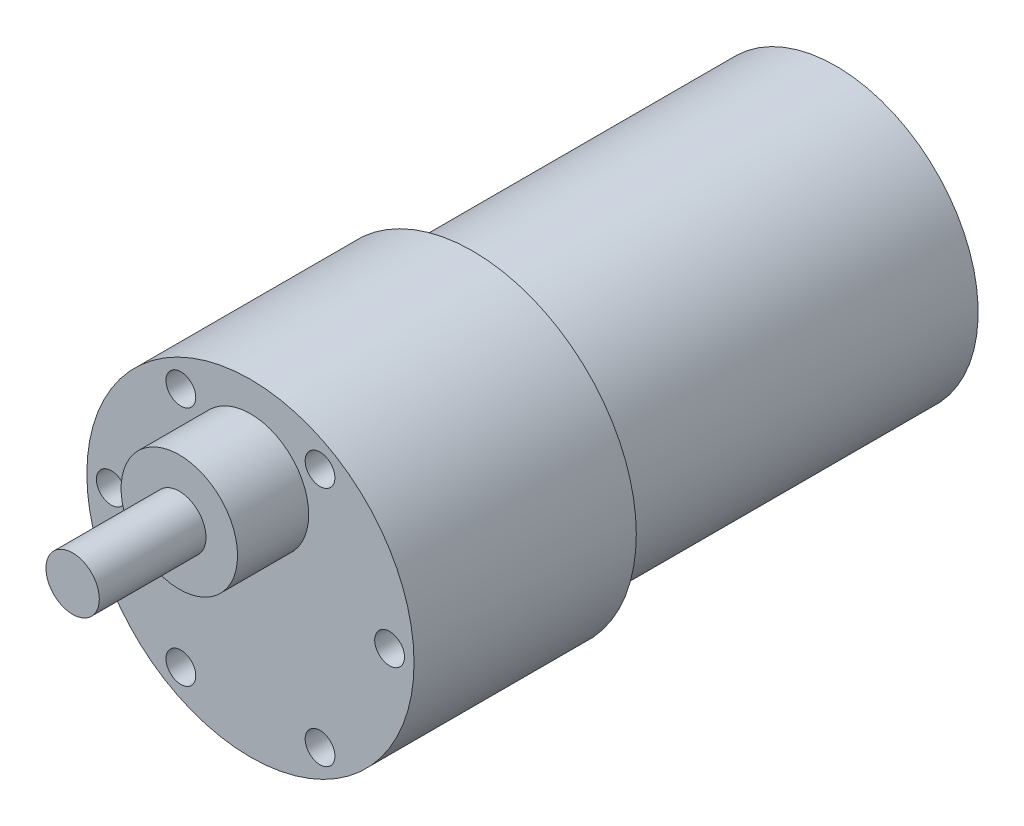
SolidWorks part; units mm, degrees
ref_plane "Front Plane" through (0, 0, 0) normal (0, 0, 1) x (1, 0, 0)
ref_plane "Top Plane" through (0, 0, 0) normal (0, 1, 0) x (1, 0, 0)
ref_plane "Right Plane" through (0, 0, 0) normal (1, 0, 0) x (0, 0, -1)
sketch "Sketch1" plane through (0, 0, 0) normal (0, 0, 1) x (1, 0, 0)
  circle A0 centre (0, 0) radius 18.4
  dimension "D1" = 36.8
extrude "Boss-Extrude1" add sketch "Sketch1" against normal blind 25
sketch "Sketch2" plane through (0, 0, -25) normal (0, 0, -1) x (-1, 0, 0)
  circle A0 centre (0, 0) radius 16
  dimension "D1" = 32
extrude "Boss-Extrude2" add sketch "Sketch2" along normal blind 40.85
sketch "Sketch3" plane through (0, 0, 0) normal (0, 0, 1) x (1, 0, 0)
  circle A0 centre (15.65, 0) radius 1.675
  circle A1 centre (7.825, -13.5533) radius 1.675
  circle A2 centre (-7.825, -13.5533) radius 1.675
  circle A3 centre (-15.65, 0) radius 1.675
  circle A4 centre (-7.825, 13.5533) radius 1.675
  circle A5 centre (7.825, 13.5533) radius 1.675
  point P5 (0, 0)
  point P6 (-11.8267, 0)
  point P15 (0, 0)
  point P16 (0, 0)
  dimension "D1" = 3.35
  dimension "D2" = 15.65
  dimension "D3" = 6
extrude "Cut-Extrude1" cut sketch "Sketch3" against normal blind 10
sketch "Sketch4" plane through (0, 0, 0) normal (0, 0, 1) x (1, 0, 0)
  circle A0 centre (0, 8.5) radius 6.55
  point P2 (0, 0)
  dimension "D2" = 13.1
  dimension "D1" = 8.5
extrude "Boss-Extrude3" add sketch "Sketch4" along normal blind 8
sketch "Sketch5" plane through (0, 0, 8) normal (0, 0, 1) x (1, 0, 0)
  circle A0 centre (0, 8.5) radius 3
  dimension "D1" = 6
extrude "Boss-Extrude4" add sketch "Sketch5" along normal blind 12
